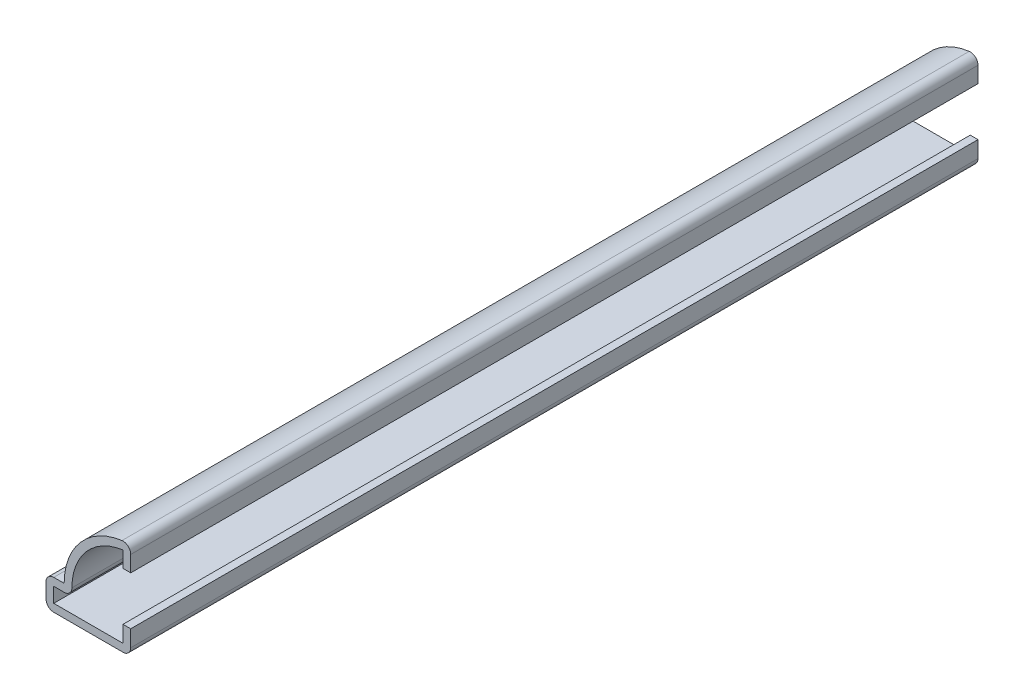
SolidWorks part; units mm, degrees
ref_plane "Front Plane" through (0, 0, 0) normal (0, 0, 1) x (1, 0, 0)
ref_plane "Top Plane" through (0, 0, 0) normal (0, 1, 0) x (1, 0, 0)
ref_plane "Right Plane" through (0, 0, 0) normal (1, 0, 0) x (0, 0, -1)
sketch "Sketch1" plane through (0, 0, 0) normal (0, 0, 1) x (1, 0, 0)
  line L6 (0, 12.7) -> (0, 9.525)
  line L7 (-11.1125, 3.9688) -> (-8.7313, 3.9688)
  line L8 (-11.1125, 0) -> (-11.1125, 3.9688)
  line L9 (0, 0) -> (-11.1125, 0)
  line L10 (0, 3.175) -> (0, 0)
  arc A1 (-8.7313, 3.9688) -> (0, 12.7) centre (0, 3.9688) cw
  point P0 (0, 0)
  dimension "D1" = 3.175
  dimension "D2" = 3.175
  dimension "D3" = 12.7
  dimension "D4" = 8.7312
  dimension "D5" = 2.3813
  dimension "D6" = 3.9688
  dimension "D7" = 11.1125
extrude "Extrude-Thin1" add sketch "Sketch1" against normal blind 111.125 thin
fillet "Fillet1" radius 1.016 5 edges at (-11.1125, 0, -55.5625) (-11.1125, 3.9688, -55.5625) (-7.6481, 2.9528, -55.5625) (0, 0, -55.5625) (0, 12.7, -55.5625)
